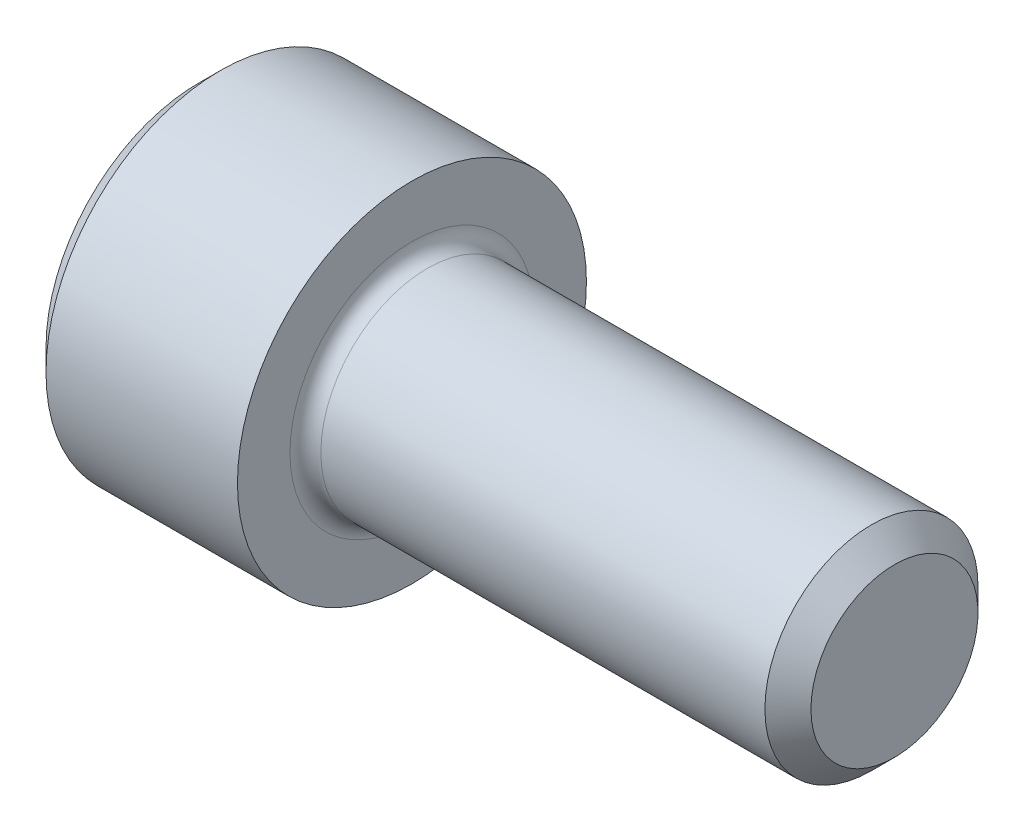
SolidWorks part; units mm, degrees
ref_plane "Plane1" through (0, 0, 0) normal (0, 0, 1) x (1, 0, 0)
ref_plane "Plane2" through (0, 0, 0) normal (0, 1, 0) x (1, 0, 0)
ref_plane "Plane3" through (0, 0, 0) normal (1, 0, 0) x (0, 0, -1)
sketch "BodySke" plane through (0, 0, 0) normal (0, 0, 1) x (1, 0, 0)
  line L0 (0, 0) -> (0, 2.5146)
  line L1 (0.3556, 2.8702) -> (3.5052, 2.8702)
  line L2 (3.5052, 2.8702) -> (3.5052, 1.7526)
  line L3 (3.5052, 1.7526) -> (11.0642, 1.7526)
  line L4 (11.4427, 1.3741) -> (11.4427, 0)
  line L5 (11.4427, 0) -> (0, 0)
  line L6 (-31.75, 0) -> (127, 0) construction
  line L7 (0, 2.5146) -> (0.3556, 2.8702)
  line L8 (11.4427, 1.3741) -> (11.0642, 1.7526)
  line L9 (0, -2.5146) -> (0.3556, -2.8702) construction
  line L10 (11.4427, -1.3741) -> (11.0642, -1.7526) construction
  line L11 (4.1402, 9.525) -> (4.1402, 3.175) construction
  line L12 (3.5052, 9.525) -> (3.5052, 3.175) construction
  line L13 (-26.6573, 9.525) -> (-26.6573, 3.175) construction
  dimension "Diameter" = 3.5052
  dimension "Head_ht" = 3.5052
  dimension "Length" = 7.9375
  dimension "Body_ch_ang" = 45
  dimension "Head_dia" = 5.7404
  dimension "Head_ch_ang" = 45
  dimension "Head_side_ht" = 3.1496
  dimension "Minor_dia" = 2.7483
  dimension "Advance" = 0.635
  dimension "Thread_nom" = 7.9375
  dimension "Thread_length" = 38.1
revolve "Base-Revolve" add sketch "BodySke"
cosmetic thread "ThreadCosmetic"
fillet "Fillet1" radius 0.254 1 edges at (3.5052, 0, 1.7526)
sketch "Sketch2" plane through (0, 0, 0) normal (0, 0, 1) x (1, 0, 0)
  line L0 (0, 1.3843) -> (1.6256, 1.3843)
  line L1 (1.6256, 1.3843) -> (2.4248, 0)
  line L2 (-31.75, 0) -> (127, 0) construction
  line L3 (2.4248, 0) -> (0, 0)
  line L4 (0, 0) -> (0, 1.3843)
  line L5 (0, 2.5146) -> (0, -2.5146) construction
  line L6 (0, 0) -> (47.625, 0) construction
  line L7 (3.5052, -2.8702) -> (3.5052, 2.8702) construction
  dimension "D1" = 1.3843
  dimension "D2" = 60
  dimension "Wall_thickness" = 1.8796
revolve "Hex-PreBroach" cut sketch "Sketch2" angle 360 about L6
sketch "Sketch3" plane through (0, 0, 0) normal (-1, 0, 0) x (0, 0.5, 0.866)
  line L0 (0.7992, 1.3843) -> (-0.7992, 1.3843)
  line L1 (-0.7992, 1.3843) -> (-1.5985, 0)
  line L2 (0.7992, 1.3843) -> (1.5985, 0)
  line L3 (0.7992, -1.3843) -> (1.5985, 0)
  line L4 (0.7992, -1.3843) -> (-0.7992, -1.3843)
  line L5 (-0.7992, -1.3843) -> (-1.5985, 0)
  dimension "D1" = 1.3843
  dimension "D2" = 1.3843
  dimension "Hex_size" = 2.7686
extrude "Hex" cut sketch "Sketch3" against normal blind 1.6256
sketch "Sketch4" plane through (0, 0, 0) normal (-1, 0, 0) x (0, 0, 1)
  line L0 (0, 0) -> (1.7399, 0)
  line L1 (0, 0) -> (6.1484, 3.5498) construction
  line L2 (0, 0) -> (0.8699, 1.5068)
  line L3 (1.4457, 0.3947) -> (1.6607, 0.5189)
  line L4 (1.0647, 1.0546) -> (1.2797, 1.1788)
  arc A0 (1.4457, 0.3947) -> (1.0647, 1.0546) centre (0, 0) ccw
  arc A1 (1.7399, 0) -> (1.6607, 0.5189) centre (0, 0) ccw
  arc A2 (0.8699, 1.5068) -> (1.2797, 1.1788) centre (0, 0) cw
  dimension "D1" = 30
  dimension "Spline_n_dim" = 2.9972
  dimension "Spline_m_dim" = 3.4798
  dimension "D2" = 60
  dimension "D3" = 0.381
  dimension "Spline_p_dim" = 0.762
extrude "Spline" [suppressed] cut sketch "Sketch4" against normal blind 1.6256
pattern_circular "CirPattern1" [suppressed] count 6 every 60
sketch "Sketch5" plane through (0, 0, 0) normal (0, 0, 1) x (1, 0, 0)
  line L0 (-31.75, 0) -> (127, 0) construction
  line L2 (0, 2.5146) -> (0, -2.5146) construction
  circle A0 centre (1.27, 0) radius 0.4445
  dimension "Drilled_hole_dia" = 0.889
  dimension "Drilled_hole_loc" = 1.27
extrude "Hole" [suppressed] cut sketch "Sketch5" against normal through all and the other way through all
pattern_circular "Drilled-4" [suppressed] count 2 every 60
pattern_circular "Drilled-6" [suppressed] count 3 every 60
sketch "ThdSchSke" plane through (0, 0, 0) normal (0, 0, 1) x (1, 0, 0)
  line L0 (4.1402, -1.3741) -> (3.8752, -1.7526)
  line L1 (4.1402, -1.3741) -> (4.4052, -1.7526)
  line L2 (4.4052, -1.7526) -> (4.4052, -2.1907)
  line L3 (-3.175, 0) -> (5.1513, 0) construction
  line L5 (4.4052, -2.1907) -> (3.8752, -2.1907)
  line L6 (3.8752, -2.1907) -> (3.8752, -1.7526)
  line L7 (0, 2.5146) -> (0, -2.5146) construction
  dimension "Thread_minor" = 2.7483
  dimension "Diameter" = 3.5052
  dimension "Start" = 4.1402
  dimension "SideAngle" = 55
  dimension "VeeAngle" = 70
  dimension "Overcut" = 4.3815
revolve "ThreadSchematic" [suppressed] cut sketch "ThdSchSke" angle 360 about L3
pattern_linear "ThdSchPat" [suppressed]
equation "\"D2@Sketch3\" = \"Hex_size@Sketch3\" / 2"
equation "\"D1@Sketch3\" = \"Hex_size@Sketch3\" / 2"
equation "\"D1@Sketch2\" = \"Hex_size@Sketch3\" / 2"
equation "\"D3@Sketch4\" = \"Spline_p_dim@Sketch4\" / 2"
equation "\"Thread_minor@ThreadCosmetic\"  =  \"Minor_dia@BodySke\""
equation "\"D2@CirPattern1\" = 360 / \"Num_teeth@CirPattern1\""
equation "\"Wall_thickness@Sketch2\" = \"Head_ht@BodySke\" - \"Key_eng@Hex\""
equation "\"Thread_length@ThreadCosmetic\" = ((sgn( (\"Length@BodySke\" - \"Advance@BodySke\" ) - \"Thread_nom@BodySke\" )-1)*( (\"Length@BodySke\" - \"Advance@BodySke\" ) - \"Thread_nom@BodySke\" ))/-2+ \"Thread_nom@BodySke\""
equation "\"Thread_minor@ThdSchSke\" = \"Minor_dia@BodySke\""
equation "\"Diameter@ThdSchSke\" = \"Diameter@BodySke\""
equation "\"Overcut@ThdSchSke\" = \"Diameter@BodySke\" * 1.25"
equation "\"Start@ThdSchSke\" = \"Head_ht@BodySke\" + \"Length@BodySke\" - \"Thread_length@ThreadCosmetic\"  '---Non-countersunk---"
equation "\"Num_threads@ThdSchPat\" = int( \"Thread_length@ThreadCosmetic\" / \"Advance@BodySke\" + 0.999 )  + 1"
equation "\"Advance@ThdSchPat\" = \"Thread_length@ThreadCosmetic\" /  (\"Num_threads@ThdSchPat\" - 1) 'relax it"
equation "\"Num_threads@ThdSchPat\" = \"Num_threads@ThdSchPat\" - sgn( \"Num_threads@ThdSchPat\" - 1) '---chamfered tips only---"
